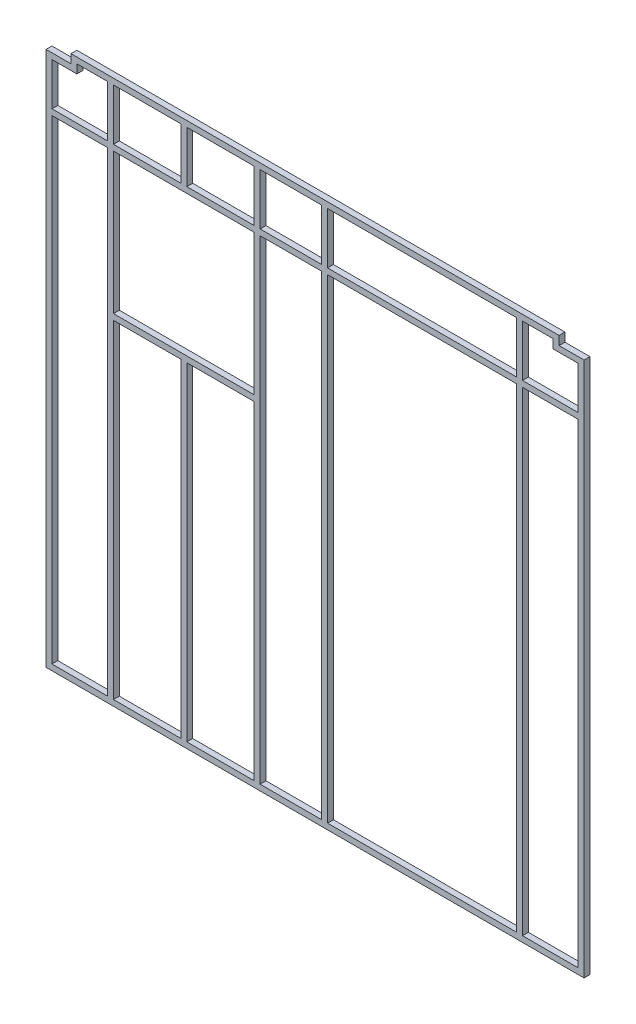
SolidWorks part; units mm, degrees
material "4032-T6"
ref_plane "Front Plane" through (0, 0, 0) normal (0, 0, 1) x (1, 0, 0)
ref_plane "Top Plane" through (0, 0, 0) normal (0, 1, 0) x (1, 0, 0)
ref_plane "Right Plane" through (0, 0, 0) normal (1, 0, 0) x (0, 0, -1)
sketch "Sketch1" plane through (0, 0, 0) normal (0, 0, 1) x (1, 0, 0)
  line L1 (-1057.021, 2356.358) -> (1057.021, 2356.358)
  line L2 (-1165.225, 2318.258) -> (-1165.225, 0)
  line L3 (-1165.225, 0) -> (1165.225, 0)
  line L4 (1165.225, 2318.258) -> (1165.225, 0)
  line L8 (1057.021, 2356.358) -> (1057.021, 2318.258)
  line L9 (1057.021, 2318.258) -> (1165.225, 2318.258)
  line L15 (-1165.225, 2318.258) -> (-1057.021, 2318.258)
  line L16 (-1057.021, 2356.358) -> (-1057.021, 2318.258)
  point P0 (0, 0)
  point P2 (0, 0)
  point P4 (0, 0)
  point P6 (0, 0)
  point P10 (0, 0)
  point P15 (0, 0)
  point P16 (0, 0)
  point P17 (0, 0)
  point P18 (0, 0)
  point P19 (0, 0)
  point P20 (0, 0)
  point P21 (0, 0)
  point P22 (0, 0)
  point P23 (0, 0)
  dimension "D1" = 2356.358
  dimension "D2" = 2330.45
  dimension "D3" = 38.1
  dimension "D4" = 108.204
  dimension "D5" = 38.1
  dimension "D6" = 108.204
sketch "Sketch2" plane through (0, 0, 0) normal (1, 0, 0) x (0, 0, -1)
  line L0 (-9.525, 22.225) -> (-9.525, 3.175)
  line L1 (-12.7, 25.4) -> (12.7, 25.4)
  line L2 (-12.7, 25.4) -> (-12.7, 0)
  line L3 (-12.7, 0) -> (12.7, 0)
  line L4 (12.7, 25.4) -> (12.7, 0)
  line L5 (-12.7, 25.4) -> (12.7, 0) construction
  line L6 (-12.7, 0) -> (12.7, 25.4) construction
  line L7 (-9.525, 3.175) -> (9.525, 3.175)
  line L8 (9.525, 22.225) -> (9.525, 3.175)
  line L9 (-9.525, 22.225) -> (9.525, 22.225)
  point P0 (0, 12.7)
  point P5 (-1.6083, -123.8768)
  point P6 (0, -489.3846)
  point P7 (-35.7051, -932.8463)
  point P8 (-50.8861, -1127.1752)
  point P9 (0, 0)
  dimension "D1" = 25.4
  dimension "D2" = 25.4
  dimension "D3" = 3.175
sweep "Sweep1" add profiles "Sketch2" path "Sketch1"
sketch "Sketch3" plane through (0, 25.4, 0) normal (0, 1, 0) x (1, 0, 0)
  line L0 (-1139.825, -12.7) -> (1139.825, -12.7) construction
  line L1 (873.125, 12.7) -> (898.525, 12.7)
  line L2 (873.125, 12.7) -> (873.125, -12.7)
  line L3 (873.125, -12.7) -> (898.525, -12.7)
  line L4 (898.525, 12.7) -> (898.525, -12.7)
  line L5 (873.125, 12.7) -> (898.525, -12.7) construction
  line L6 (873.125, -12.7) -> (898.525, 12.7) construction
  line L8 (-1139.825, 12.7) -> (1139.825, 12.7) construction
  line L9 (876.3, 9.525) -> (876.3, -9.525)
  line L10 (876.3, -9.525) -> (895.35, -9.525)
  line L11 (895.35, 9.525) -> (895.35, -9.525)
  line L12 (876.3, 9.525) -> (895.35, 9.525)
  line L13 (-581.025, 12.7) -> (-555.625, 12.7)
  line L14 (-581.025, 12.7) -> (-581.025, -12.7)
  line L15 (-581.025, -12.7) -> (-555.625, -12.7)
  line L16 (-555.625, 12.7) -> (-555.625, -12.7)
  line L17 (-581.025, 12.7) -> (-555.625, -12.7) construction
  line L18 (-581.025, -12.7) -> (-555.625, 12.7) construction
  line L19 (-577.85, 9.525) -> (-577.85, -9.525)
  line L20 (-577.85, -9.525) -> (-558.8, -9.525)
  line L21 (-558.8, 9.525) -> (-558.8, -9.525)
  line L22 (-577.85, 9.525) -> (-558.8, 9.525)
  line L23 (-898.525, 12.7) -> (-873.125, 12.7)
  line L24 (-898.525, 12.7) -> (-898.525, -12.7)
  line L25 (-898.525, -12.7) -> (-873.125, -12.7)
  line L26 (-873.125, 12.7) -> (-873.125, -12.7)
  line L27 (-898.525, 12.7) -> (-873.125, -12.7) construction
  line L28 (-898.525, -12.7) -> (-873.125, 12.7) construction
  line L29 (-895.35, 9.525) -> (-895.35, -9.525)
  line L30 (-895.35, -9.525) -> (-876.3, -9.525)
  line L31 (-876.3, 9.525) -> (-876.3, -9.525)
  line L32 (-895.35, 9.525) -> (-876.3, 9.525)
  line L33 (-1139.825, -12.7) -> (-1139.825, 12.7) construction
  line L34 (28.575, 12.7) -> (53.975, 12.7)
  line L35 (28.575, 12.7) -> (28.575, -12.7)
  line L36 (28.575, -12.7) -> (53.975, -12.7)
  line L37 (53.975, 12.7) -> (53.975, -12.7)
  line L38 (28.575, 12.7) -> (53.975, -12.7) construction
  line L39 (28.575, -12.7) -> (53.975, 12.7) construction
  line L40 (31.75, 9.525) -> (31.75, -9.525)
  line L41 (31.75, -9.525) -> (50.8, -9.525)
  line L42 (50.8, 9.525) -> (50.8, -9.525)
  line L43 (31.75, 9.525) -> (50.8, 9.525)
  line L44 (-263.525, 12.7) -> (-238.125, 12.7)
  line L45 (-263.525, 12.7) -> (-263.525, -12.7)
  line L46 (-263.525, -12.7) -> (-238.125, -12.7)
  line L47 (-238.125, 12.7) -> (-238.125, -12.7)
  line L48 (-263.525, 12.7) -> (-238.125, -12.7) construction
  line L49 (-263.525, -12.7) -> (-238.125, 12.7) construction
  line L50 (-260.35, 9.525) -> (-260.35, -9.525)
  line L51 (-260.35, -9.525) -> (-241.3, -9.525)
  line L52 (-241.3, 9.525) -> (-241.3, -9.525)
  line L53 (-260.35, 9.525) -> (-241.3, 9.525)
  line L54 (1139.825, -12.7) -> (1139.825, 12.7) construction
  point P0 (885.825, 0)
  point P15 (-568.325, 0)
  point P24 (-885.825, 0)
  point P35 (0, 0)
  point P36 (0, 0)
  point P37 (0, 0)
  point P38 (0, 0)
  point P39 (0, 0)
  point P40 (0, 0)
  point P41 (0, 0)
  point P42 (0, 0)
  point P43 (0, 0)
  point P44 (0, 0)
  point P45 (41.275, 0)
  point P54 (-250.825, 0)
  point P63 (-255.9058, 0)
  dimension "D2" = 25.4
  dimension "D3" = 3.175
  dimension "D4" = 25.4
  dimension "D5" = 25.4
  dimension "D6" = 254
  dimension "D7" = 3.175
  dimension "D8" = 317.5
  dimension "D9" = 3.175
  dimension "D10" = 25.4
  dimension "D11" = 25.4
  dimension "D12" = 3.175
  dimension "D13" = 292.1
  dimension "D14" = 3.175
  dimension "D15" = 317.5
  dimension "D16" = 254
extrude "Boss-Extrude1" add sketch "Sketch3" along normal up to surface (2305.558 mm away) separate body up to face at (0, 2330.958, 0)
sketch "Sketch5" plane through (1031.621, 0, 0) normal (-1, 0, 0) x (0, 0, 1)
  line L0 (12.7, 2292.858) -> (12.7, 2330.958) construction
  line L1 (-12.7, 2108.2) -> (12.7, 2108.2)
  line L2 (-12.7, 2108.2) -> (-12.7, 2082.8)
  line L3 (-12.7, 2082.8) -> (12.7, 2082.8)
  line L4 (12.7, 2108.2) -> (12.7, 2082.8)
  line L5 (-12.7, 2108.2) -> (12.7, 2082.8) construction
  line L6 (-12.7, 2082.8) -> (12.7, 2108.2) construction
  line L7 (-12.7, 2292.858) -> (-12.7, 2330.958) construction
  line L8 (12.7, 25.4) -> (-12.7, 25.4) construction
  line L9 (-9.525, 2105.025) -> (-9.525, 2085.975)
  line L10 (-9.525, 2085.975) -> (9.525, 2085.975)
  line L11 (9.525, 2105.025) -> (9.525, 2085.975)
  line L12 (-9.525, 2105.025) -> (9.525, 2105.025)
  point P0 (0, 2095.5)
  dimension "D1" = 25.4
  dimension "D2" = 2070.1
  dimension "D3" = 3.175
extrude "Boss-Extrude2" add sketch "Sketch5" along normal up to surface and the other way up to surface
sketch "Sketch6" plane through (0, 0, 12.7) normal (0, 0, 1) x (1, 0, 0)
  line L1 (-873.125, 2082.8) -> (-263.525, 2082.8)
  line L2 (-873.125, 2082.8) -> (-873.125, 1447.8)
  line L3 (-873.125, 1447.8) -> (-263.525, 1447.8)
  line L4 (-263.525, 2082.8) -> (-263.525, 1447.8)
  line L5 (-873.125, 2082.8) -> (-263.525, 1447.8) construction
  line L6 (-873.125, 1447.8) -> (-263.525, 2082.8) construction
  line L7 (-873.125, 2082.8) -> (-581.025, 2082.8) construction
  line L8 (-873.125, 2082.8) -> (-873.125, 25.4) construction
  point P0 (-568.325, 1765.3)
  dimension "D1" = 609.6
  dimension "D2" = 635
extrude "Cut-Extrude1" cut sketch "Sketch6" against normal up to surface (25.4 mm away)
sketch "Sketch7" plane through (-873.125, 0, 0) normal (1, 0, 0) x (0, 0, -1)
  line L0 (12.7, 2082.8) -> (12.7, 25.4) construction
  line L1 (-12.7, 1473.2) -> (12.7, 1473.2)
  line L2 (-12.7, 1473.2) -> (-12.7, 1447.8)
  line L3 (-12.7, 1447.8) -> (12.7, 1447.8)
  line L4 (12.7, 1473.2) -> (12.7, 1447.8)
  line L5 (-12.7, 1473.2) -> (12.7, 1447.8) construction
  line L6 (-12.7, 1447.8) -> (12.7, 1473.2) construction
  line L7 (-12.7, 2082.8) -> (-12.7, 25.4) construction
  line L8 (12.7, 2082.8) -> (-12.7, 2082.8) construction
  point P0 (0, 1460.5)
  point P9 (0, 330.441)
  dimension "D1" = 25.4
  dimension "D2" = 609.6
extrude "Boss-Extrude3" add sketch "Sketch7" along normal up to surface (609.6 mm away) up to face at (-263.525, 1054.1, 0)
